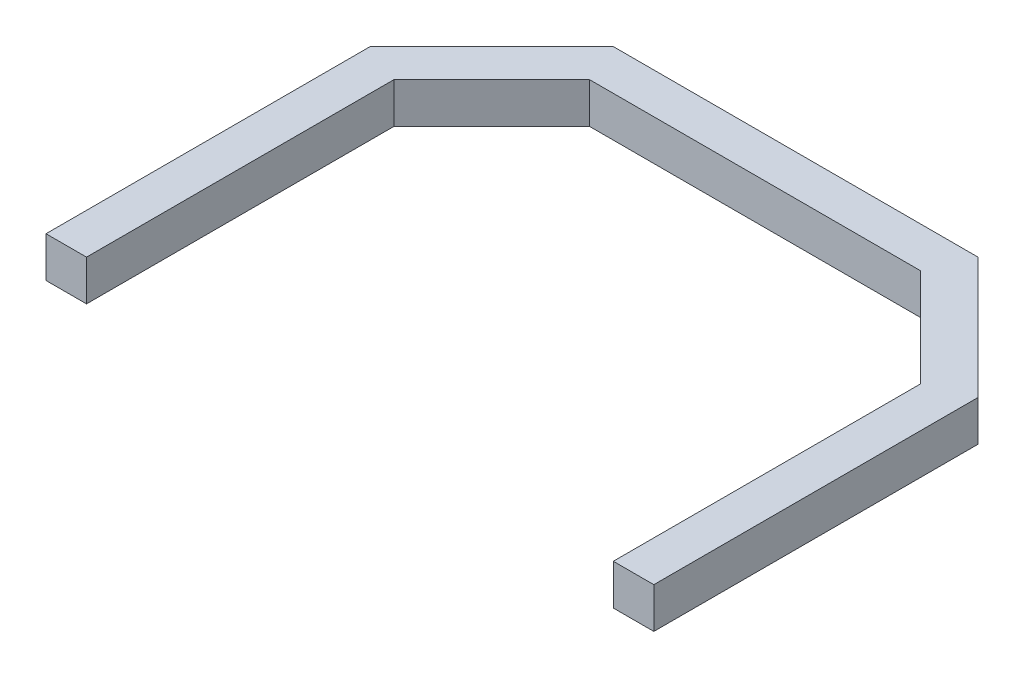
SolidWorks part; units mm, degrees
ref_plane "Front Plane" through (0, 0, 0) normal (0, 0, 1) x (1, 0, 0)
ref_plane "Top Plane" through (0, 0, 0) normal (0, 1, 0) x (1, 0, 0)
ref_plane "Right Plane" through (0, 0, 0) normal (1, 0, 0) x (0, 0, -1)
sketch "Sketch1" plane through (0, 0, 0) normal (0, 1, 0) x (1, 0, 0)
  line L0 (-39.0153, -6.0566) -> (-24.0153, 8.9434)
  line L1 (-24.0153, 8.9434) -> (20.9847, 8.9434)
  line L2 (-39.0153, -6.0566) -> (-39.0153, -46.0566)
  line L3 (-34.0153, -8.1277) -> (-34.0153, -46.0566)
  line L4 (35.9847, -6.0566) -> (35.9847, -46.0566)
  line L5 (20.9847, 8.9434) -> (35.9847, -6.0566)
  line L6 (-34.0153, -8.1277) -> (-21.9442, 3.9434)
  line L7 (-21.9442, 3.9434) -> (18.9137, 3.9434)
  line L8 (18.9137, 3.9434) -> (30.9847, -8.1277)
  line L9 (30.9847, -8.1277) -> (30.9847, -46.0566)
  line L10 (35.9847, -46.0566) -> (30.9847, -46.0566)
  line L11 (-34.0153, -46.0566) -> (-39.0153, -46.0566)
  point P0 (-39.0153, 8.9434)
  point P3 (35.9847, 8.9434)
  dimension "D1" = 75
  dimension "D2" = 55
  dimension "D4" = 55
  dimension "D3" = 5
extrude "Boss-Extrude1" add sketch "Sketch1" along normal blind 5
